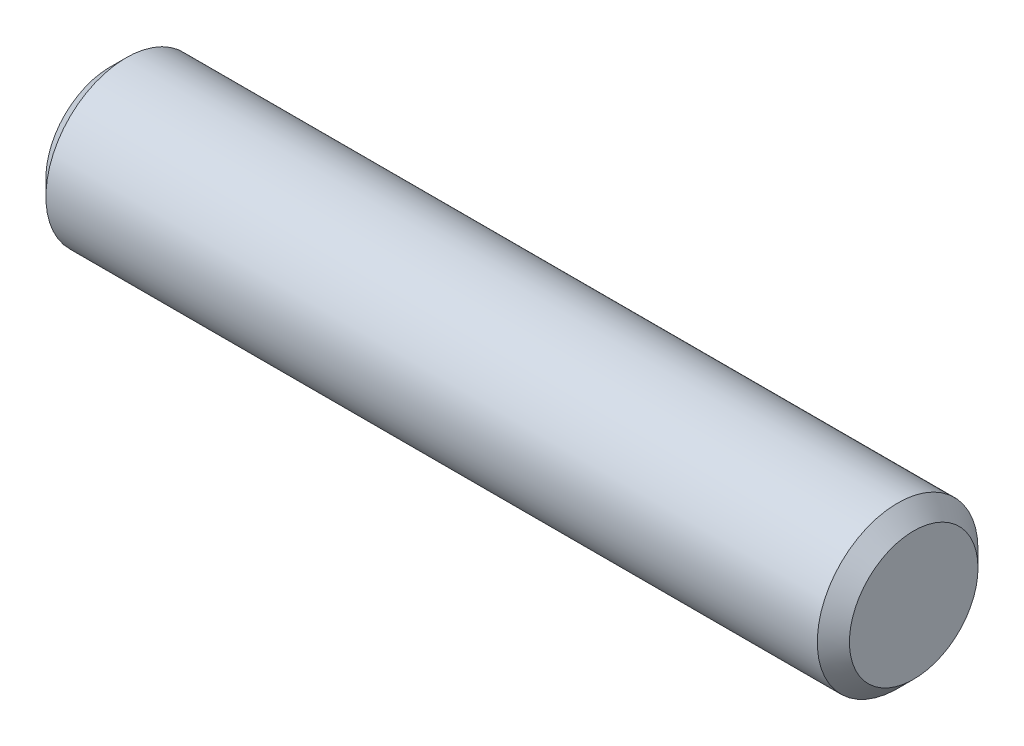
SolidWorks part; units mm, degrees
ref_plane "Front Plane" through (0, 0, 0) normal (0, 0, 1) x (1, 0, 0)
ref_plane "Top Plane" through (0, 0, 0) normal (0, 1, 0) x (1, 0, 0)
ref_plane "Right Plane" through (0, 0, 0) normal (1, 0, 0) x (0, 0, -1)
sketch "Sketch1" plane through (0, 0, 0) normal (0, 0, 1) x (1, 0, 0)
  line L0 (-7.9375, 0) -> (7.9375, 0) construction
  line L1 (-7.9375, 1.5875) -> (-7.9375, -1.5875) construction
  line L2 (7.9375, 1.5875) -> (7.9375, -1.5875) construction
  dimension "Diameter" = 3.175
  dimension "Length" = 15.875
sketch "Sketch2" plane through (0, 0, 0) normal (1, 0, 0) x (0, 0, -1)
  circle A0 centre (0, 0) radius 1.5875
extrude "Extrude1" add sketch "Sketch2" against normal up to vertex (7.9375 mm away) and the other way up to vertex (7.9375 mm away) up to point (-7.9375, 0, 0) other way up to point (7.9375, 0, 0)
chamfer "Chamfer1" distance 0.3175 angle 45 2 edges at (7.9375, 0, -1.5875) (-7.9375, 0, -1.5875)
equation "\"D1@Chamfer1\" = \"Diameter@Sketch1\"*.1"
